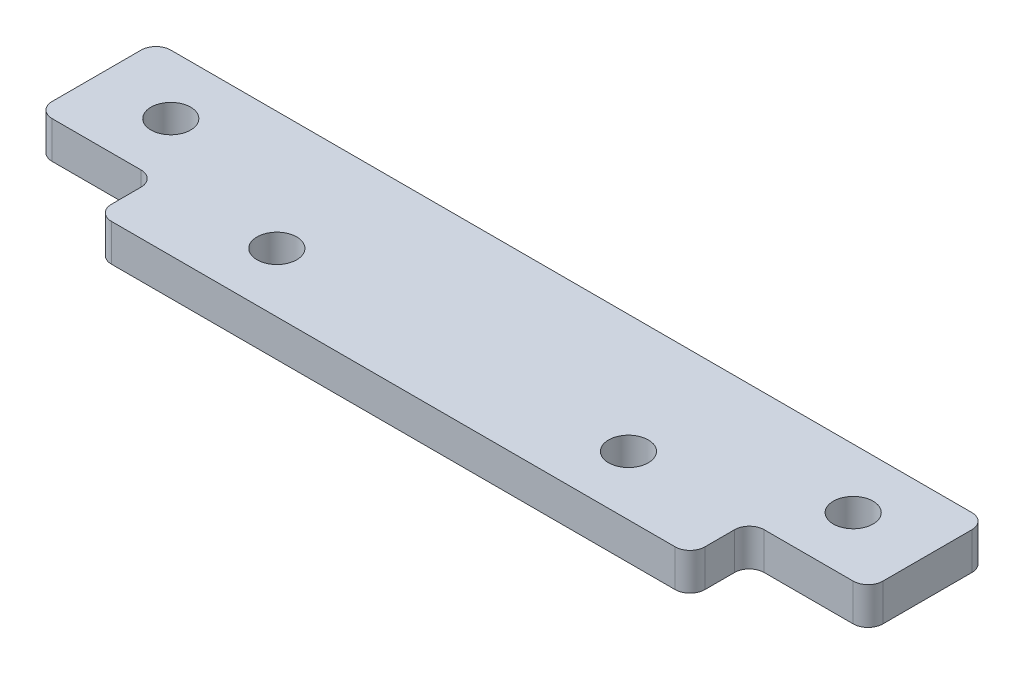
SolidWorks part; units mm, degrees
ref_plane "Front Plane" through (0, 0, 0) normal (0, 0, 1) x (1, 0, 0)
ref_plane "Top Plane" through (0, 0, 0) normal (0, 1, 0) x (1, 0, 0)
ref_plane "Right Plane" through (0, 0, 0) normal (1, 0, 0) x (0, 0, -1)
sketch "Sketch1" plane through (0, 0, 0) normal (0, 1, 0) x (1, 0, 0)
  line L0 (0, 0) -> (50.8, 0)
  line L1 (50.8, 0) -> (50.8, 5.08)
  line L2 (50.8, 5.08) -> (60.96, 5.08)
  line L3 (60.96, 5.08) -> (60.96, 15.24)
  line L4 (25.4, 0) -> (25.4, 45.6771) construction
  line L5 (0, 0) -> (0, 5.08)
  line L6 (0, 5.08) -> (-10.16, 5.08)
  line L7 (-10.16, 5.08) -> (-10.16, 15.24)
  line L8 (-10.16, 15.24) -> (60.96, 15.24)
  dimension "D1" = 50.8
  dimension "D2" = 71.12
  dimension "D3" = 5.08
  dimension "D4" = 10.16
extrude "Boss-Extrude1" add sketch "Sketch1" along normal blind 3.175
sketch "Sketch2" plane through (0, 3.175, 0) normal (0, 1, 0) x (1, 0, 0)
  line L0 (25.4, 0) -> (25.4, 30.6047) construction
  line L1 (0, 0) -> (50.8, 0) construction
  point P4 (10.3505, 5.08)
  point P5 (40.4495, 5.08)
  point P6 (-3.81, 10.16)
  point P7 (54.61, 10.16)
  dimension "D1" = 30.099
  dimension "D2" = 5.08
  dimension "D3" = 58.42
  dimension "D4" = 5.08
hole_wizard "M3 Clearance Hole2" positions "Sketch6" profile "Sketch5" hole size "M3" standard "ANSI Metric" end condition through all
sketch "Sketch6" plane through (0, 3.175, 0) normal (0, 1, 0) x (1, 0, 0)
  point P0 (-3.81, 10.16)
  point P3 (10.3505, 5.08)
  point P6 (40.4495, 5.08)
  point P9 (54.61, 10.16)
sketch "Sketch5" plane through (-3.81, 3.175, -10.16) normal (1, 0, 0) x (0, 0, 1)
  line L0 (0, 0) -> (0, 3.175)
  line L1 (0, 3.175) -> (1.7, 3.175)
  line L2 (1.7, 3.175) -> (1.7, 0)
  line L5 (1.7, 0) -> (0, 0)
  line L11 (0, -6.35) -> (0, 107.95) construction
  dimension "Thru Hole Dia." = 3.4
  dimension "Thru Hole Depth" = 3.175
fillet "Fillet1" radius 1.27 8 edges at (60.96, 1.5875, -15.24) (60.96, 1.5875, -5.08) (50.8, 1.5875, -5.08) (50.8, 1.5875, 0) (-10.16, 1.5875, -15.24) (-10.16, 1.5875, -5.08) (0, 1.5875, -5.08) (0, 1.5875, 0)
sketch "Sketch7" plane through (0, 3.175, 0) normal (0, 1, 0) x (1, 0, 0)
  line L0 (10.3505, 6.78) -> (11.1125, 6.78)
  line L1 (11.1125, 3.38) -> (10.3505, 3.38)
  line L2 (25.4, 0) -> (25.4, 21.0099) construction
  line L3 (25.4, 0) -> (25.4, 30.6047) construction
  line L4 (39.6875, 3.38) -> (40.4495, 3.38)
  line L5 (40.4495, 6.78) -> (39.6875, 6.78)
  circle A0 centre (10.3505, 5.08) radius 1.7 construction
  arc A1 (11.1125, 6.78) -> (11.1125, 3.38) centre (11.1125, 5.08) cw
  arc A2 (10.3505, 6.78) -> (10.3505, 3.38) centre (10.3505, 5.08) ccw
  arc A3 (39.6875, 6.78) -> (39.6875, 3.38) centre (39.6875, 5.08) ccw
  arc A4 (40.4495, 6.78) -> (40.4495, 3.38) centre (40.4495, 5.08) cw
  dimension "D1" = 28.575
extrude "Cut-Extrude1" [suppressed] cut sketch "Sketch7" against normal through all
